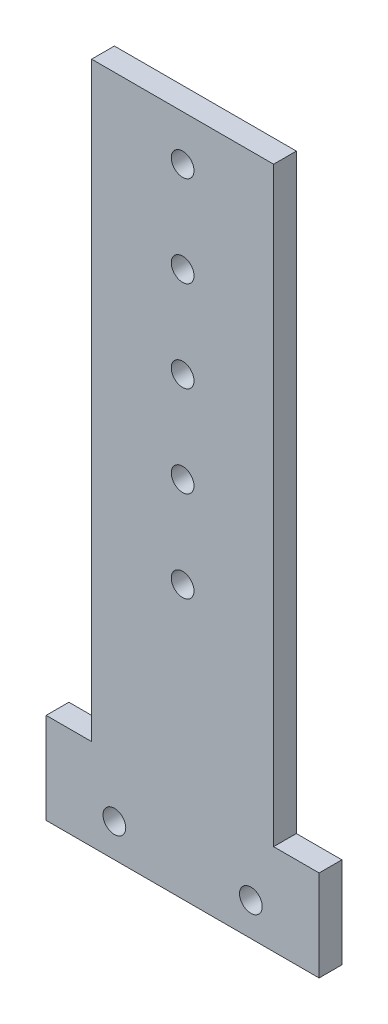
SolidWorks part; units mm, degrees
material "AISI 1020"
ref_plane "Front Plane" through (0, 0, 0) normal (0, 0, 1) x (1, 0, 0)
ref_plane "Top Plane" through (0, 0, 0) normal (0, 1, 0) x (1, 0, 0)
ref_plane "Right Plane" through (0, 0, 0) normal (1, 0, 0) x (0, 0, -1)
sketch "Sketch1" plane through (0, 0, 0) normal (0, 0, 1) x (1, 0, 0)
  line L0 (25.4, 0) -> (25.4, 178.5062) construction
  line L2 (0, 13.5062) -> (0, 178.5062)
  line L4 (50.8, 13.5062) -> (50.8, 178.5062)
  line L5 (0, 13.5062) -> (-12.7, 13.5062)
  line L6 (63.5, 13.5062) -> (50.8, 13.5062)
  line L7 (63.5, 13.5062) -> (63.5, -11.8938)
  line L8 (63.5, -11.8938) -> (-12.7, -11.8938)
  line L9 (-12.7, 13.5062) -> (-12.7, -11.8938)
  line L10 (50.8, 178.5062) -> (0, 178.5062)
  circle A0 centre (6.35, -2.6048) radius 3.175
  circle A1 centre (44.45, -2.6048) radius 3.175
  circle A2 centre (25.4, 165.8062) radius 3.175
  circle A3 centre (25.4, 140.4062) radius 3.175
  circle A4 centre (25.4, 115.0062) radius 3.175
  circle A5 centre (25.4, 89.6062) radius 3.175
  circle A6 centre (25.4, 64.2062) radius 3.175
  point P1 (25.4, 185.9688)
  dimension "D1" = 6.35
  dimension "D2" = 6.35
  dimension "D7" = 6.35
  dimension "D8" = 165
  dimension "D10" = 6.35
  dimension "D11" = 6.35
  dimension "D12" = 6.35
  dimension "D13" = 6.35
  dimension "D3" = 38.1
  dimension "D4" = 6.35
  dimension "D5" = 12.7
  dimension "D6" = 12.7
  dimension "D9" = 25.4
  dimension "D14" = 25.4
  dimension "D15" = 25.4
  dimension "D16" = 25.4
  dimension "D17" = 25.4
  dimension "D18" = 12.7
extrude "Boss-Extrude1" add sketch "Sketch1" along normal blind 6.35
